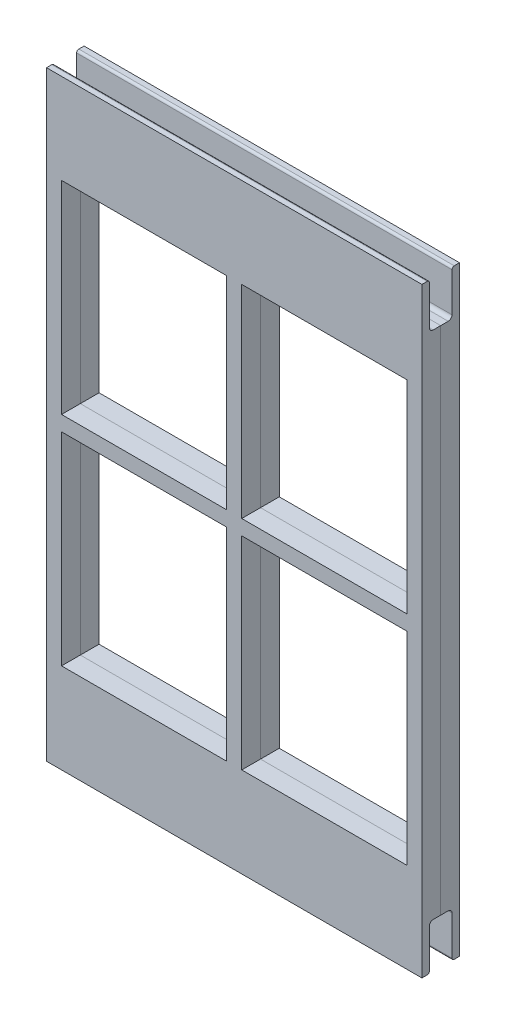
SolidWorks part; units mm, degrees
ref_plane "Plano frontal" through (0, 0, 0) normal (0, 0, 1) x (1, 0, 0)
ref_plane "Plano superior" through (0, 0, 0) normal (0, 1, 0) x (1, 0, 0)
ref_plane "Plano direito" through (0, 0, 0) normal (1, 0, 0) x (0, 0, -1)
sketch "Esboço1" plane through (0, 0, 0) normal (0, 0, 1) x (1, 0, 0)
  line L0 (7.037, 30.1321) -> (7.037, -25.8704)
  line L1 (-17.963, 32.1296) -> (32.037, 32.1296)
  line L2 (-17.963, 32.1296) -> (-17.963, 3.1296)
  line L3 (-17.963, -37.8704) -> (32.037, -37.8704)
  line L4 (32.037, 32.1296) -> (32.037, -27.8704)
  line L5 (-17.963, -27.8704) -> (32.037, -27.8704)
  line L6 (-17.963, -27.8704) -> (-17.963, -37.8704)
  line L7 (-17.963, -37.8704) -> (32.037, -37.8704)
  line L8 (30.037, 2.1296) -> (8.037, 2.1296)
  line L9 (32.037, -27.8704) -> (32.037, -37.8704)
  line L10 (8.037, 3.1296) -> (30.037, 3.1296)
  line L11 (6.037, 32.1296) -> (8.037, 32.1296)
  line L12 (6.037, 30.1321) -> (6.037, -25.8704)
  line L13 (6.037, -27.8704) -> (8.037, -27.8704)
  line L14 (8.037, 30.1321) -> (8.037, -25.8704)
  line L15 (-15.963, 3.1296) -> (6.037, 3.1296)
  line L16 (-17.963, 42.1296) -> (32.037, 42.1296)
  line L17 (-15.963, 1.1296) -> (6.037, 1.1296)
  line L18 (32.037, 3.1296) -> (32.037, 1.1296)
  line L19 (-17.963, 32.1296) -> (-15.963, 32.1296)
  line L20 (-17.963, 32.1296) -> (-17.963, 3.1296)
  line L21 (-17.963, -27.8704) -> (-15.963, -27.8704)
  line L22 (-15.963, 30.1321) -> (-15.963, -25.8704)
  line L23 (-17.963, -27.8704) -> (32.037, -27.8704)
  line L24 (-17.963, -27.8704) -> (-17.963, -25.8704)
  line L25 (-15.963, -25.8704) -> (30.037, -25.8704)
  line L26 (32.037, -27.8704) -> (32.037, -25.8704)
  line L27 (32.037, -27.8704) -> (30.037, -27.8704)
  line L28 (32.037, -27.8704) -> (32.037, 32.1296)
  line L29 (32.037, 32.1296) -> (30.037, 32.1296)
  line L30 (30.037, -25.8704) -> (30.037, 30.1321)
  line L31 (-17.963, 32.1296) -> (32.037, 32.1296)
  line L32 (-17.963, 32.1296) -> (-17.963, 30.1321)
  line L33 (-15.963, 30.1321) -> (30.037, 30.1321)
  line L34 (32.037, 32.1296) -> (32.037, 30.1321)
  line L35 (6.037, 2.1296) -> (-15.963, 2.1296)
  line L36 (8.037, 1.1296) -> (30.037, 1.1296)
  line L37 (-17.963, 1.1296) -> (-17.963, -37.8704)
  line L38 (-17.963, 1.1296) -> (-17.963, -27.8704)
  line L39 (-17.963, 1.1296) -> (-17.963, 3.1296)
  line L40 (32.037, 32.1296) -> (32.037, 42.1296)
  line L41 (-17.963, 32.1296) -> (32.037, 32.1296)
  line L42 (-17.963, 32.1296) -> (-17.963, 42.1296)
  dimension "D1" = 50
  dimension "D2" = 70
  dimension "D3" = 10
  dimension "D4" = 1
  dimension "D5" = 1
  dimension "D6" = 1
  dimension "D7" = 1
  dimension "D8" = 2
  dimension "D9" = 2
  dimension "D10" = 2
extrude "Ressalto-extrusão1" add sketch "Esboço1" along normal blind 5 contours L39 L37 L24 L5 L23 L4 L28 L1 L2 L20 L22 L33 L30 L25 | L9 L23 L5 L6 L3 | L33 L0 L25 L14 | L33 L12 L25 L0 | L8 L30 L10 L14 | L14 L36 L30 L8 | L35 L12 L15 L22 | L12 L35 L22 L17 | L42 L1 L40 L16
sketch "Esboço2" plane through (0, 0, 0) normal (1, 0, 0) x (0, 0, -1)
  line L0 (-5, 2.1296) -> (0, 2.1296)
  line L1 (-2.5, -37.8704) -> (-2.5, -31.8704)
  line L2 (-5, -37.8704) -> (0, -37.8704) construction
  line L3 (-2.5, -31.8704) -> (-4, -31.8704)
  line L4 (-2.5, -31.8704) -> (-2.5, -37.8704)
  line L5 (-2.5, -37.8704) -> (-4, -37.8704)
  line L6 (-4, -31.8704) -> (-4, -37.8704)
  line L7 (-2.5, -31.8704) -> (-1, -31.8704)
  line L8 (-2.5, -31.8704) -> (-2.5, -37.8704)
  line L9 (-2.5, -37.8704) -> (-1, -37.8704)
  line L10 (-1, -31.8704) -> (-1, -37.8704)
  line L11 (-5, 42.1296) -> (-5, -37.8704) construction
  line L12 (0, 42.1296) -> (0, -37.8704) construction
  line L13 (-2.5, 42.1296) -> (-1, 42.1296)
  line L14 (-2.5, 42.1296) -> (-4, 42.1296)
  line L15 (-4, 36.1296) -> (-4, 42.1296)
  line L16 (-2.5, 42.1296) -> (-2.5, 36.1296)
  line L17 (-1, 36.1296) -> (-1, 42.1296)
  line L18 (-2.5, 36.1296) -> (-1, 36.1296)
  line L19 (-2.5, 36.1296) -> (-4, 36.1296)
  dimension "D1" = 1.5
  dimension "D2" = 1.5
  dimension "D3" = 6
extrude "Corte-extrusão2" cut sketch "Esboço2" against normal through all both and the other way through all contours L3 L6 L5 L1 | L10 L7 L1 L9 | L19 L16 L14 L15 | L16 L18 L17 L13
fillet "Filete3" radius 0.5 4 edges at (7.037, -31.8704, 1) (7.037, -31.8704, 4) (7.037, 36.1296, 1) (7.037, 36.1296, 4)
fillet "Filete4" radius 0.3 4 edges at (7.037, -37.8704, 1) (7.037, -37.8704, 4) (7.037, 42.1296, 1) (7.037, 42.1296, 4)
sketch "Esboço4" plane through (0, 0, 0) normal (0, 1, 0) x (1, 0, 0)
  line L0 (-17.963, -2.5) -> (32.037, -2.5)
  line L1 (-17.963, -1.5) -> (-17.963, -3.5) construction
  line L2 (32.037, -1.5) -> (32.037, -3.5) construction
split "Dividir1" trim tools "Esboço4" bodies to split 103 resulting bodies 106 107
